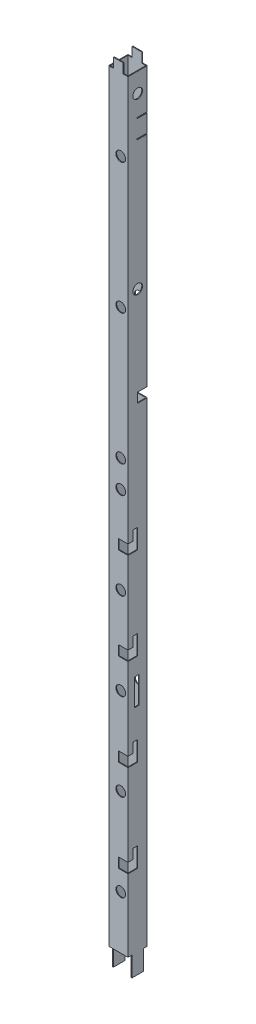
SolidWorks part; units mm, degrees
ref_plane "Front Plane" through (0, 0, 0) normal (0, 0, 1) x (1, 0, 0)
ref_plane "Top Plane" through (0, 0, 0) normal (0, 1, 0) x (1, 0, 0)
ref_plane "Right Plane" through (0, 0, 0) normal (1, 0, 0) x (0, 0, -1)
sketch "Sketch1" plane through (0, 0, 0) normal (0, 1, 0) x (1, 0, 0)
  line L0 (1.5, 1.5) -> (38.5, 1.5)
  line L1 (0.5, 0) -> (39.5, 0)
  line L2 (0, 0.5) -> (0, 39.5)
  line L3 (0.5, 40) -> (39.5, 40)
  line L4 (40, 0.5) -> (40, 39.5)
  line L5 (38.5, 1.5) -> (38.5, 38.5)
  line L6 (1.5, 38.5) -> (38.5, 38.5)
  line L7 (1.5, 1.5) -> (1.5, 38.5)
  arc A0 (39.5, 0) -> (40, 0.5) centre (39.5, 0.5) ccw
  arc A1 (0.5, 0) -> (0, 0.5) centre (0.5, 0.5) cw
  arc A2 (0, 39.5) -> (0.5, 40) centre (0.5, 39.5) cw
  arc A3 (39.5, 40) -> (40, 39.5) centre (39.5, 39.5) cw
  arc A4 (38.5, 1.5) -> (38.5, 1.5) centre (38.5, 1.5) ccw
  arc A5 (38.5, 38.5) -> (38.5, 38.5) centre (38.5, 38.5) cw
  arc A6 (1.5, 38.5) -> (1.5, 38.5) centre (1.5, 38.5) cw
  arc A7 (1.5, 1.5) -> (1.5, 1.5) centre (1.5, 1.5) cw
  point P9 (0, 0)
  dimension "D3" = 0.5
  dimension "D1" = 40
  dimension "D2" = 40
  dimension "D4" = 1.5
extrude "Boss-Extrude1" add sketch "Sketch1" along normal blind 1637.5
sketch "Sketch2" plane through (0, 0, -40) normal (0, 0, 1) x (1, 0, 0)
  line L0 (0.5, 1637.5) -> (39.5, 1637.5) construction
  line L11 (30, 1637.5) -> (40, 1637.5)
  line L12 (30, 1637.5) -> (30, 1617.5)
  line L13 (30, 1617.5) -> (40, 1617.5)
  line L14 (40, 1637.5) -> (40, 1617.5)
  line L15 (40, 1637.5) -> (40, 0) construction
  line L16 (20, 1637.5) -> (20, 1571.1839) construction
  line L17 (0, 1637.5) -> (0, 1617.5)
  line L18 (10, 1617.5) -> (0, 1617.5)
  line L19 (10, 1637.5) -> (10, 1617.5)
  line L20 (10, 1637.5) -> (0, 1637.5)
  dimension "D1" = 20
  dimension "D2" = 10
extrude "Cut-Extrude1" cut sketch "Sketch2" along normal blind 40
sketch "Sketch3" plane through (40, 0, 0) normal (1, 0, 0) x (0, 0, -1)
  line L0 (40, 1617.5) -> (40, 0) construction
  line L1 (40, 1535) -> (19, 1535)
  line L2 (40, 1535) -> (40, 1533)
  line L3 (40, 1533) -> (19, 1533)
  line L4 (19, 1535) -> (19, 1533)
  line L5 (0.5, 1617.5) -> (39.5, 1617.5) construction
  line L6 (40, 1515) -> (25.1946, 1515) construction
  line L7 (40, 1617.5) -> (40, 0) construction
  line L8 (19, 1495) -> (19, 1497)
  line L9 (40, 1497) -> (19, 1497)
  line L10 (40, 1495) -> (40, 1497)
  line L11 (40, 1495) -> (19, 1495)
  point P9 (20, 1617.5)
  dimension "D1" = 2
  dimension "D2" = 82.5
  dimension "D3" = 21
  dimension "D4" = 20
extrude "Cut-Extrude2" cut sketch "Sketch3" against normal blind 20
sketch "Sketch4" plane through (0, 0, 0) normal (-1, 0, 0) x (0, 0, 1)
  line L0 (-20, 0) -> (-20, 31.3131) construction
  line L1 (0, 0) -> (-8.1, 0)
  line L2 (0, 0) -> (0, 41)
  line L3 (0, 41) -> (-8.1, 41)
  line L4 (-8.1, 0) -> (-8.1, 41)
  line L5 (-39.5, 0) -> (-0.5, 0) construction
  line L6 (-31.9, 0) -> (-31.9, 41)
  line L7 (-40, 41) -> (-31.9, 41)
  line L8 (-40, 0) -> (-40, 41)
  line L9 (-40, 0) -> (-31.9, 0)
  dimension "D1" = 8.1
  dimension "D2" = 41
extrude "Cut-Extrude3" cut sketch "Sketch4" against normal through all
sketch "Sketch5" plane through (40, 0, -40) normal (-1, 0, 0) x (0, 0, 1)
  line L0 (40, 190.5) -> (20, 190.5)
  line L1 (39.5, 41) -> (31.9, 41) construction
  line L2 (20, 190.5) -> (20, 231)
  line L3 (20, 231) -> (30, 231)
  line L4 (30, 231) -> (30, 211)
  line L5 (30, 211) -> (40, 211)
  line L7 (40, 211) -> (40, 190.5)
  line L9 (40, 380.5) -> (20, 380.5)
  line L10 (20, 380.5) -> (20, 421)
  line L11 (20, 421) -> (30, 421)
  line L12 (30, 421) -> (30, 401)
  line L13 (30, 401) -> (40, 401)
  line L14 (40, 401) -> (40, 380.5)
  line L15 (40, 570.5) -> (20, 570.5)
  line L16 (20, 570.5) -> (20, 611)
  line L17 (20, 611) -> (30, 611)
  line L18 (30, 611) -> (30, 591)
  line L19 (30, 591) -> (40, 591)
  line L20 (40, 591) -> (40, 570.5)
  line L21 (40, 760.5) -> (20, 760.5)
  line L22 (20, 760.5) -> (20, 801)
  line L23 (20, 801) -> (30, 801)
  line L24 (30, 801) -> (30, 781)
  line L25 (30, 781) -> (40, 781)
  line L26 (40, 781) -> (40, 760.5)
  line L27 (40, 1617.5) -> (40, 41) construction
  dimension "D1" = 20
  dimension "D2" = 10
  dimension "D3" = 20
  dimension "D4" = 20.5
  dimension "D5" = 170
  dimension "D6" = 4
extrude "Cut-Extrude4" cut sketch "Sketch5" along normal blind 20
sketch "Sketch6" plane through (0, 0, -40) normal (0, 0, -1) x (-1, 0, 0)
  line L0 (-40, 1495) -> (-40, 41) construction
  line L1 (-40, 1043) -> (-20, 1043)
  line L2 (-40, 1043) -> (-40, 1023)
  line L3 (-40, 1023) -> (-20, 1023)
  line L4 (-20, 1043) -> (-20, 1023)
  line L5 (-39.5, 41) -> (-0.5, 41) construction
  dimension "D1" = 982
  dimension "D2" = 20
  dimension "D3" = 20
extrude "Cut-Extrude5" cut sketch "Sketch6" against normal blind 20
sketch "Sketch7" plane through (40, 0, 0) normal (1, 0, 0) x (0, 0, -1)
  line L0 (0.5, 1617.5) -> (39.5, 1617.5) construction
  circle A0 centre (20, 1577.5) radius 10
  circle A1 centre (20, 1227.5) radius 10
  point P5 (20, 1617.5)
  dimension "D1" = 40
  dimension "D2" = 20
  dimension "D3" = 350
extrude "Cut-Extrude6" cut sketch "Sketch7" against normal through all
sketch "Sketch8" plane through (0, 0, 0) normal (0, 0, 1) x (1, 0, 0)
  line L0 (40, 1617.5) -> (40, 781) construction
  line L1 (30, 1617.5) -> (39.5, 1617.5) construction
  line L2 (40, 380.5) -> (40, 211) construction
  line L3 (39.5, 41) -> (0.5, 41) construction
  circle A0 centre (25, 1467.5) radius 10
  circle A1 centre (25, 1197.5) radius 10
  circle A2 centre (25, 927.5) radius 10
  circle A3 centre (25, 151) radius 10
  circle A4 centre (25, 331) radius 10
  circle A5 centre (25, 511) radius 10
  circle A6 centre (25, 691) radius 10
  circle A7 centre (25, 871) radius 10
  dimension "D1" = 15
  dimension "D2" = 20
  dimension "D3" = 150
  dimension "D4" = 3
  dimension "D5" = 20
  dimension "D6" = 15
  dimension "D7" = 110
  dimension "D8" = 5
extrude "Cut-Extrude7" cut sketch "Sketch8" against normal through all
sketch "Sketch9" plane through (40, 0, 0) normal (1, 0, 0) x (0, 0, -1)
  line L0 (0, 570.5) -> (0, 401) construction
  line L1 (13, 481) -> (23, 481)
  line L2 (13, 481) -> (13, 536)
  line L3 (13, 536) -> (23, 536)
  line L4 (23, 481) -> (23, 536)
  line L5 (31.9, 41) -> (39.5, 41) construction
  dimension "D1" = 13
  dimension "D2" = 55
  dimension "D3" = 10
  dimension "D4" = 440
extrude "Cut-Extrude8" cut sketch "Sketch9" against normal blind 10
